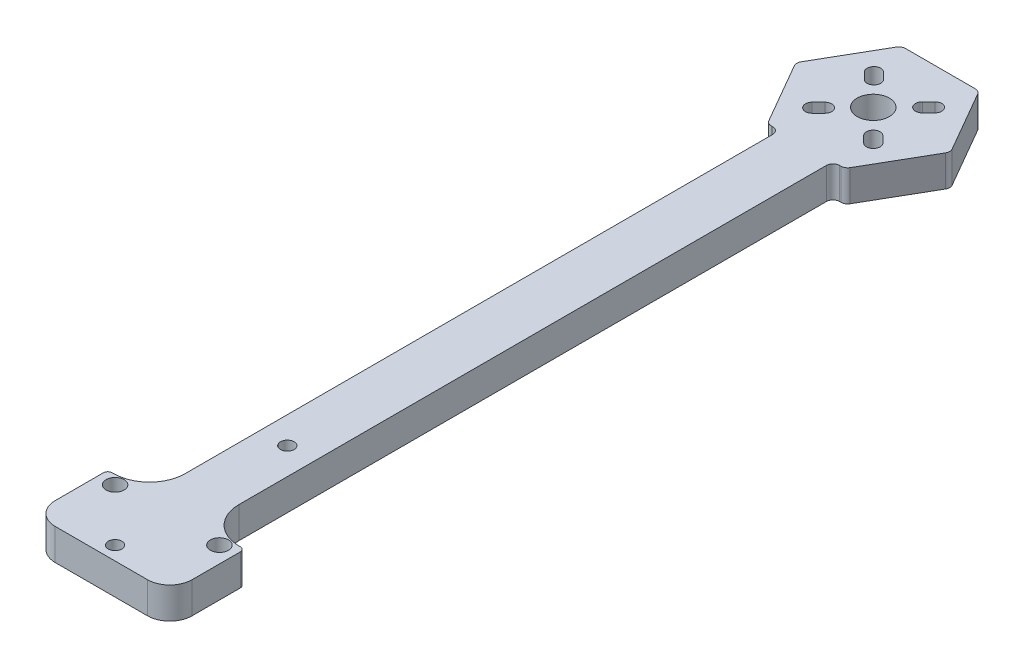
SolidWorks part; units mm, degrees
material "Thornel Mat VMA"
ref_plane "前视基准面" through (0, 0, 0) normal (0, 0, 1) x (1, 0, 0)
ref_plane "上视基准面" through (0, 0, 0) normal (0, 1, 0) x (1, 0, 0)
ref_plane "右视基准面" through (0, 0, 0) normal (1, 0, 0) x (0, 0, -1)
other "Configuration Table"
sketch "草图1" plane through (0, 0, 0) normal (0, 1, 0) x (1, 0, 0)
  line L0 (12, 0) -> (12, -0.0024)
  line L1 (0, 0) -> (12, 0)
  line L2 (0, 0) -> (0, 140.81)
  line L3 (0, 140.81) -> (12, 140.81)
  line L4 (12, 0) -> (12, 140.81)
  line L5 (-9.3063, -0.0024) -> (21.3085, -0.0024)
  line L6 (-9.3063, -0.0024) -> (-9.3063, -16.7665)
  line L7 (-9.3063, -16.7665) -> (21.3085, -16.7665)
  line L8 (21.3085, -0.0024) -> (21.3085, -16.7665)
  line L9 (-18.063, 181.9962) -> (30.3554, 181.9962)
  line L10 (-18.063, 181.9962) -> (-18.063, 140.81)
  line L11 (-18.063, 140.81) -> (30.3554, 140.81)
  line L12 (30.3554, 181.9962) -> (30.3554, 140.81)
  line L13 (12, -0.0024) -> (12, 0)
  line L14 (0, 0) -> (0, -0.0024)
  line L15 (0, -0.0024) -> (12, -0.0024)
  line L16 (12, 24.8103) -> (6, 24.8103) construction
  circle A3 centre (6, 24.8103) radius 1.52
  dimension "D1" = 140.81
  dimension "D3" = 6
  dimension "D2" = 12
extrude "凸台-拉伸1" add sketch "草图1" along normal blind 7 contours L8 L5 L1 L6 L7 | L1 L4 L3 L2 | L12 L9 L10 L11 L3 | L1 L14 L5 L0
sketch "草图2" plane through (0, 7, 0) normal (0, 1, 0) x (1, 0, 0)
  line L1 (-18.063, 140.81) -> (30.3554, 140.81)
  line L2 (-18.063, 140.81) -> (-18.063, 181.9962)
  line L3 (-18.063, 181.9962) -> (30.3554, 181.9962)
  line L4 (30.3554, 140.81) -> (30.3554, 181.9962)
  line L5 (14.6603, 140.81) -> (23.3205, 155.81)
  line L6 (23.3205, 155.81) -> (14.6603, 170.81)
  line L7 (14.6603, 170.81) -> (-2.6603, 170.81)
  line L8 (-2.6603, 170.81) -> (-11.3205, 155.81)
  line L9 (-11.3205, 155.81) -> (-2.6603, 140.81)
  line L10 (-2.6603, 140.81) -> (14.6603, 140.81)
  line L11 (6, 155.81) -> (16.9808, 144.8292)
  line L12 (12.8943, 148.9157) -> (13.9691, 149.9905)
  line L13 (13.9691, 149.9905) -> (12.5549, 151.4047)
  line L14 (12.5549, 151.4047) -> (11.4801, 150.3299)
  line L15 (11.8195, 147.8409) -> (10.4053, 149.2551)
  line L16 (11.8195, 163.7791) -> (10.4053, 162.3649)
  line L17 (13.9691, 161.6295) -> (12.5549, 160.2153)
  line L18 (-1.8229, 161.6295) -> (-0.4087, 160.2153)
  line L19 (6, 155.81) -> (23.3205, 155.81)
  line L20 (0.3267, 163.7791) -> (1.7409, 162.3649)
  line L21 (-1.8229, 149.9905) -> (-0.4087, 151.4047)
  line L22 (0.3267, 147.8409) -> (1.7409, 149.2551)
  line L23 (6, 155.81) -> (6, 24.8103)
  line L24 (6, -55.409) -> (6, 24.8103)
  circle A0 centre (6, 155.81) radius 15 construction
  circle A1 centre (6, 155.81) radius 3.6
  circle A4 centre (11.4801, 150.3299) radius 1.52
  circle A5 centre (12.8943, 148.9157) radius 1.52
  circle A6 centre (11.4801, 161.2901) radius 1.52
  circle A7 centre (12.8943, 162.7043) radius 1.52
  circle A8 centre (-0.7481, 162.7043) radius 1.52
  circle A9 centre (0.6661, 161.2901) radius 1.52
  circle A10 centre (-0.7481, 148.9157) radius 1.52
  circle A11 centre (0.6661, 150.3299) radius 1.52
  circle A12 centre (6, -55.409) radius 7.7097
  dimension "D3" = 7.75
  dimension "D8" = 130.9997
  dimension "D1" = 180
  dimension "D4" = 9.75
  dimension "D5" = 90
  dimension "D6" = 90
  dimension "D7" = 1.52
extrude "切除-拉伸2" cut sketch "草图2" against normal blind 10
fillet "圆角1" radius 8 2 edges at (12, 3.5, 0.0024) (0, 3.5, 0.0024)
fillet "圆角3" radius 1 2 edges at (21.3085, 3.5, 0.0024) (-9.3063, 3.5, 0.0024)
fillet "圆角4" radius 5 2 edges at (-9.3063, 3.5, 16.7665) (21.3085, 3.5, 16.7665)
fillet "圆角5" radius 1.5 8 edges at (14.6603, 3.5, -170.81) (23.3205, 3.5, -155.81) (14.6603, 3.5, -140.81) (12, 3.5, -140.81) (0, 3.5, -140.81) (-2.6603, 3.5, -170.81) (-11.3205, 3.5, -155.81) (-2.6603, 3.5, -140.81)
sketch "草图3" plane through (0, 0, 0) normal (0, -1, 0) x (-1, 0, 0)
  circle A0 centre (-17.6673, -2.0224) radius 2.02
  circle A1 centre (5.6673, -2.0224) radius 2.02
  circle A2 centre (-6, -13.6897) radius 1.52
extrude "切除-拉伸3" cut sketch "草图3" against normal blind 10
ref_plane "基准面1" through (6, 0, 0) normal (-1, 0, 0) x (0, 0, 1)
